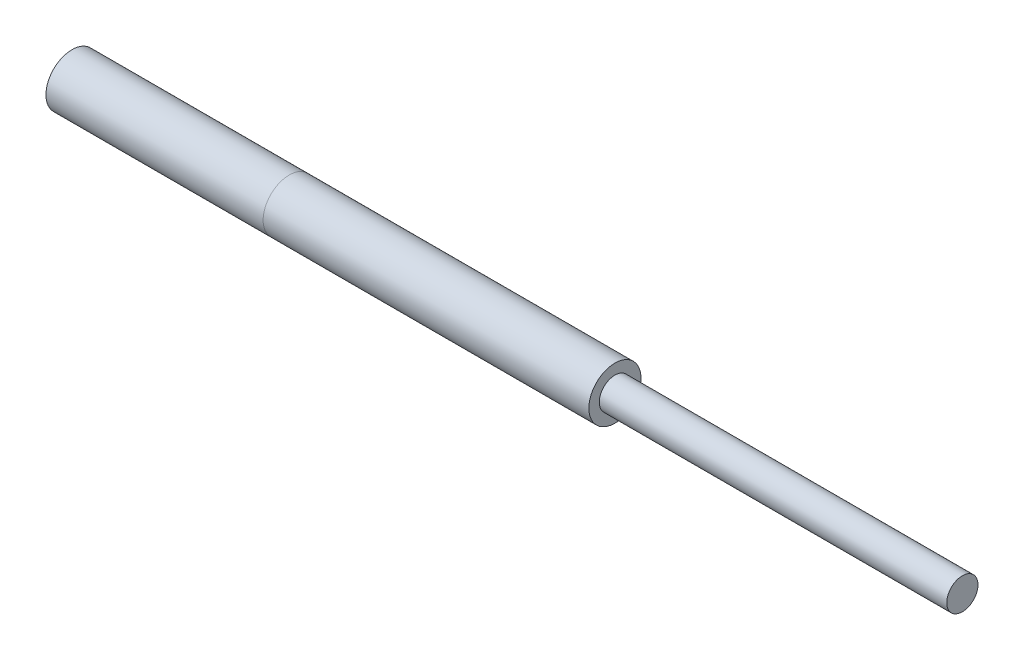
SolidWorks part; units mm, degrees
ref_plane "Front Plane" through (0, 0, 0) normal (0, 0, 1) x (1, 0, 0)
ref_plane "Top Plane" through (0, 0, 0) normal (0, 1, 0) x (1, 0, 0)
ref_plane "Right Plane" through (0, 0, 0) normal (1, 0, 0) x (0, 0, -1)
sketch "Sketch1" plane through (0, 0, 0) normal (1, 0, 0) x (0, 0, -1)
  circle A0 centre (0, 0) radius 30
  circle A1 centre (0, 0) radius 20
  dimension "D1" = 60
  dimension "D2" = 40
extrude "Boss-Extrude1" add sketch "Sketch1" along normal blind 250
sketch "Sketch2" plane through (250, 0, 0) normal (1, 0, 0) x (0, 0, -1)
  circle A0 centre (0, 0) radius 30
  dimension "D1" = 60
extrude "Boss-Extrude2" add sketch "Sketch2" along normal blind 375 separate body
sketch "Sketch3" plane through (625, 0, 0) normal (1, 0, 0) x (0, 0, -1)
  circle A0 centre (0, 0) radius 18
  dimension "D1" = 36
extrude "Boss-Extrude3" add sketch "Sketch3" along normal blind 400 separate body
